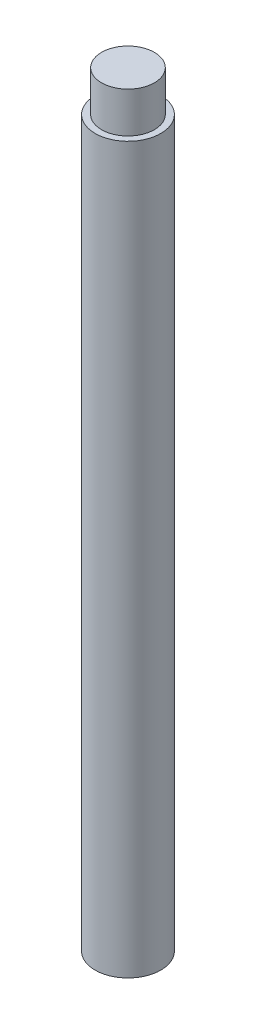
SolidWorks part; units mm, degrees
material "Hexcel AS4C (3000 Filaments)"
ref_plane "Front Plane" through (0, 0, 0) normal (0, 0, 1) x (1, 0, 0)
ref_plane "Top Plane" through (0, 0, 0) normal (0, 1, 0) x (1, 0, 0)
ref_plane "Right Plane" through (0, 0, 0) normal (1, 0, 0) x (0, 0, -1)
sketch "Sketch1" plane through (0, 0, 0) normal (0, 1, 0) x (1, 0, 0)
  circle A0 centre (0, 0) radius 4
  circle A1 centre (0, 0) radius 4.85
  dimension "D1" = 9.7
  dimension "D2" = 8
extrude "Boss-Extrude1" add sketch "Sketch1" along normal mid plane 105
sketch "Sketch2" plane through (0, 52.5, 0) normal (0, 1, 0) x (1, 0, 0)
  circle A0 centre (0, 0) radius 3.9
  dimension "D1" = 7.8
extrude "Boss-Extrude2" add sketch "Sketch2" along normal blind 8 separate body
sketch "Sketch3" plane through (0, 52.5, 0) normal (0, 1, 0) x (1, 0, 0)
  circle A0 centre (0, 0) radius 4.85
  circle A1 centre (0, 0) radius 4.85 construction
extrude "Boss-Extrude3" add sketch "Sketch3" along normal blind 2
chamfer "Chamfer1" distance 4 angle 45 1 edges at (0, 52.5, 4)
sketch "Sketch4" plane through (0, -52.5, 0) normal (0, -1, 0) x (1, 0, 0)
  circle A1 centre (0, 0) radius 4.85
  circle A2 centre (0, 0) radius 4.85
  dimension "D1" = 0
extrude "Boss-Extrude4" add sketch "Sketch4" against normal up to surface (107 mm away) contours A2 up to face at (0, 54.5, 3.9)
sketch "Sketch5" plane through (0, -52.5, 0) normal (0, -1, 0) x (1, 0, 0)
  circle A0 centre (0, 0) radius 4
  dimension "D1" = 8
extrude "Cut-Extrude1" cut sketch "Sketch5" against normal blind 14
chamfer "Chamfer2" distance 3.9 angle 45 1 edges at (0, -38.5, -4)
